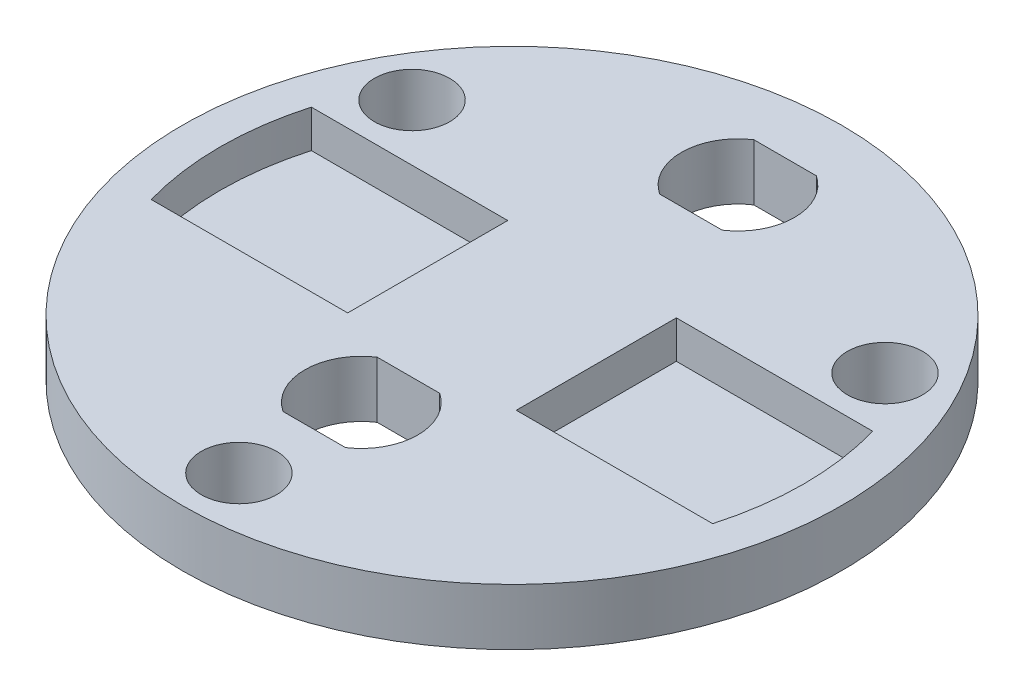
SolidWorks part; units mm, degrees
ref_plane "Alzado" through (0, 0, 0) normal (0, 0, 1) x (1, 0, 0)
ref_plane "Planta" through (0, 0, 0) normal (0, 1, 0) x (1, 0, 0)
ref_plane "Vista lateral" through (0, 0, 0) normal (1, 0, 0) x (0, 0, -1)
sketch "Croquis1" plane through (0, 0, 0) normal (0, 1, 0) x (1, 0, 0)
  circle A0 centre (0, 0) radius 17.5
  circle A1 centre (0, 0) radius 13.5
  dimension "D1" = 35
  dimension "D2" = 4
extrude "Saliente-Extruir1" add sketch "Croquis1" along normal blind 3 contours A1 | A0 A1
sketch "Croquis2" plane through (0, 3, 0) normal (0, 1, 0) x (1, 0, 0)
  line L0 (0, 0) -> (-17.5, 0)
  line L1 (0, 0) -> (0, 17.5)
  line L2 (-16.9761, -4.25) -> (-4.4761, -4.25)
  line L3 (-4.4761, -4.25) -> (-4.4761, 4.25)
  line L4 (-16.9761, 4.25) -> (-4.4761, 4.25)
  line L5 (16.9761, 4.25) -> (4.4761, 4.25)
  line L6 (4.4761, -4.25) -> (4.4761, 4.25)
  line L7 (16.9761, -4.25) -> (4.4761, -4.25)
  circle A0 centre (0, 0) radius 17.5
  circle A1 centre (0, 0) radius 15.5
  point P9 (-4.4761, 0)
  point P14 (4.4761, 0)
  dimension "D1" = 4.25
  dimension "D2" = 12.5
  dimension "D3" = 2
extrude "Cortar-Extruir1" cut sketch "Croquis2" against normal blind 2 contours L4 A1 L0 L3 | L0 A1 L2 L3 | L7 A1 L5 L6
sketch "Croquis3" plane through (0, 0, 0) normal (0, -1, 0) x (-1, 0, 0)
  line L0 (0, 17.5) -> (0, -17.5)
  line L3 (0, -14.5) -> (12.5574, 7.25)
  line L4 (12.5574, 7.25) -> (-12.5574, 7.25)
  line L5 (-12.5574, 7.25) -> (0, -14.5)
  circle A0 centre (0, 0) radius 17.5
  circle A1 centre (0, -14.5) radius 2
  circle A2 centre (12.5574, 7.25) radius 2
  circle A3 centre (0, 0) radius 14.5
  circle A4 centre (-12.5574, 7.25) radius 2
  dimension "D1" = 4
  dimension "D3" = 35
  dimension "D4" = 3
  dimension "D5" = 4
  dimension "D6" = 4
  dimension "D7" = 29
  dimension "D2" = 60
extrude "Cortar-Extruir2" cut sketch "Croquis3" against normal through all
sketch "Croquis4" plane through (0, 0, 0) normal (0, -1, 0) x (-1, 0, 0)
  line L0 (0, 17.5) -> (0, -17.5)
  line L1 (1.6583, 14.5) -> (-1.6583, 14.5)
  line L2 (1.6583, 9.5) -> (-1.6583, 9.5)
  line L3 (1.6583, -5.5) -> (-1.6583, -5.5)
  line L4 (-1.6583, -10.5) -> (1.6583, -10.5)
  circle A0 centre (0, 0) radius 17.5
  arc A1 (1.6583, 9.5) -> (1.6583, 14.5) centre (0, 12) ccw
  arc A2 (1.6583, -10.5) -> (1.6583, -5.5) centre (0, -8) ccw
  arc A3 (-1.6583, -5.5) -> (-1.6583, -10.5) centre (0, -8) ccw
  arc A4 (-1.6583, 14.5) -> (-1.6583, 9.5) centre (0, 12) ccw
  dimension "D1" = 6
  dimension "D2" = 6
  dimension "D3" = 2.5
  dimension "D4" = 2.5
  dimension "D5" = 2.5
  dimension "D6" = 2.5
  dimension "D7" = 12
  dimension "D8" = 8
extrude "Cortar-Extruir3" cut sketch "Croquis4" against normal blind 10 contours L1 A4 L2 A1 | L3 A3 L4 A2
